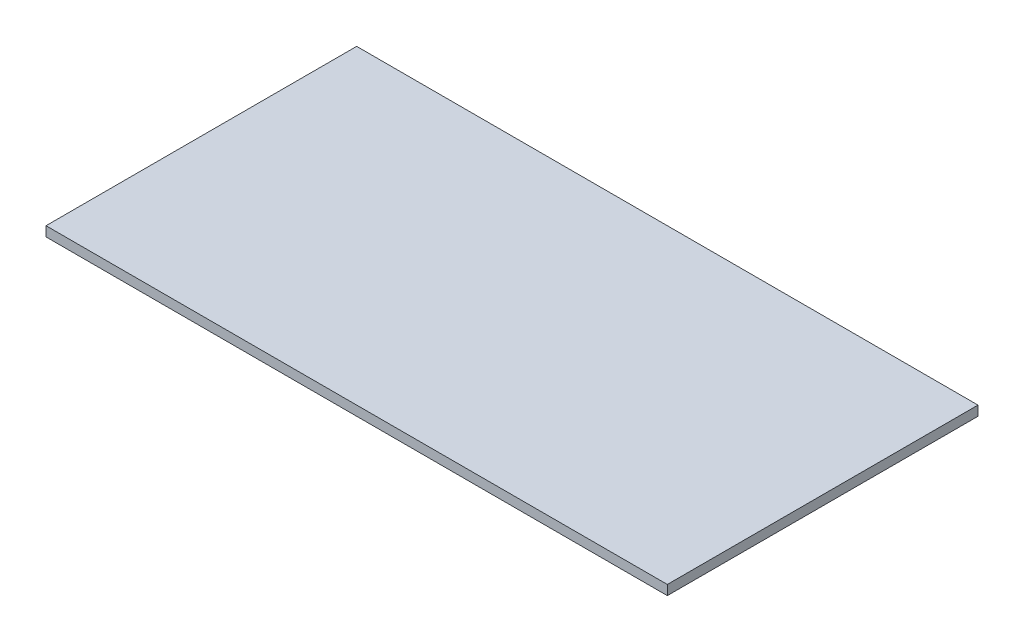
SolidWorks part; units mm, degrees
material "Pine"
ref_plane "Front Plane" through (0, 0, 0) normal (0, 0, 1) x (1, 0, 0)
ref_plane "Top Plane" through (0, 0, 0) normal (0, 1, 0) x (1, 0, 0)
ref_plane "Right Plane" through (0, 0, 0) normal (1, 0, 0) x (0, 0, -1)
sketch "Sketch1" plane through (0, 0, 0) normal (0, 1, 0) x (1, 0, 0)
  line L0 (-609.6, 304.8) -> (609.6, -304.8) construction
  line L1 (-609.6, 304.8) -> (609.6, 304.8)
  line L2 (-609.6, 304.8) -> (-609.6, -304.8)
  line L3 (-609.6, -304.8) -> (609.6, -304.8)
  line L4 (609.6, 304.8) -> (609.6, -304.8)
  dimension "D1" = 609.6
  dimension "D2" = 1219.2
extrude "Boss-Extrude1" add sketch "Sketch1" along normal blind 19.05
